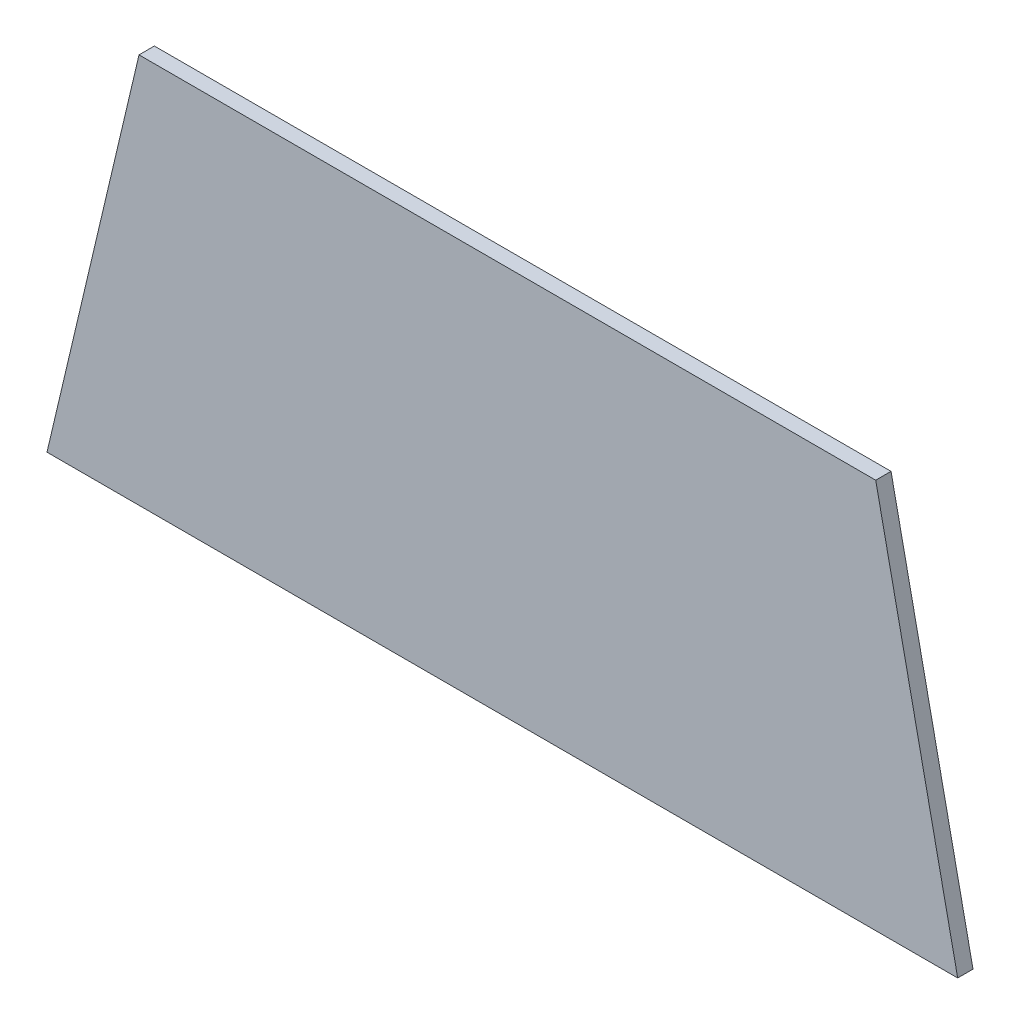
SolidWorks part; units mm, degrees
ref_plane "Plan de face" through (0, 0, 0) normal (0, 0, 1) x (1, 0, 0)
ref_plane "Plan de dessus" through (0, 0, 0) normal (0, 1, 0) x (1, 0, 0)
ref_plane "Plan de droite" through (0, 0, 0) normal (1, 0, 0) x (0, 0, -1)
sketch "Esquisse1" plane through (0, 0, 0) normal (0, 0, 1) x (1, 0, 0)
  line L0 (96.3137, -237.357) -> (80.2702, -161.0019)
  line L1 (80.2702, -161.0019) -> (-63.909, -161.0019)
  line L2 (-63.909, -161.0019) -> (-81.9215, -237.357)
  line L3 (-81.9215, -237.357) -> (96.3137, -237.357)
  line L4 (95.9478, -237.2251) -> (79.901, -160.8545) construction
  point P3 (74.5282, -101.8085)
  point P4 (79.6816, -161.0019)
  point P9 (75.6618, -161.0019)
extrude "Boss.-Extru.1" add sketch "Esquisse1" along normal blind 3
